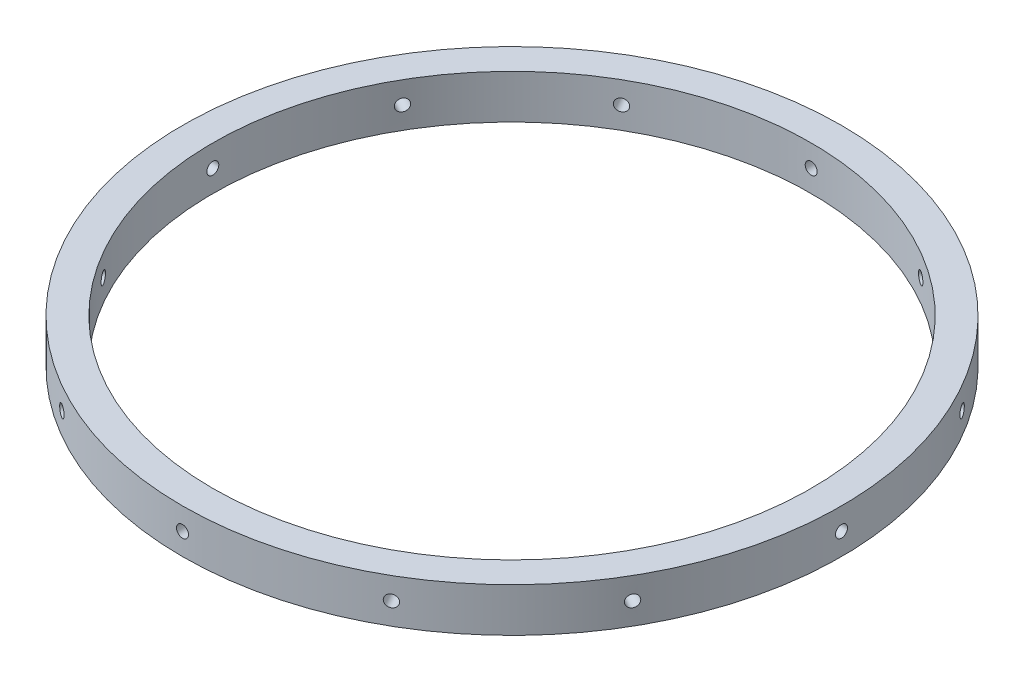
SolidWorks part; units mm, degrees
ref_plane "Front Plane" through (0, 0, 0) normal (0, 0, 1) x (1, 0, 0)
ref_plane "Top Plane" through (0, 0, 0) normal (0, 1, 0) x (1, 0, 0)
ref_plane "Right Plane" through (0, 0, 0) normal (1, 0, 0) x (0, 0, -1)
sketch "Sketch1" plane through (0, 0, 0) normal (0, 1, 0) x (1, 0, 0)
  circle A0 centre (0, 0) radius 95.25
  circle A1 centre (0, 0) radius 86.487
  dimension "D1" = 190.5
  dimension "D2" = 172.974
extrude "Boss-Extrude1" add sketch "Sketch1" along normal blind 12.7
sketch "Sketch3" plane through (0, 0, 0) normal (0, 0, 1) x (1, 0, 0)
  circle A0 centre (0, 6.35) radius 1.7272
  dimension "D1" = 3.4544
  dimension "D2" = 6.35
extrude "Cut-Extrude2" cut sketch "Sketch3" against normal blind 254
pattern_circular "CirPattern1" count 12 over 360 about axis through (0, 12.7, 0) along (0, 1, 0) of "Cut-Extrude2"
